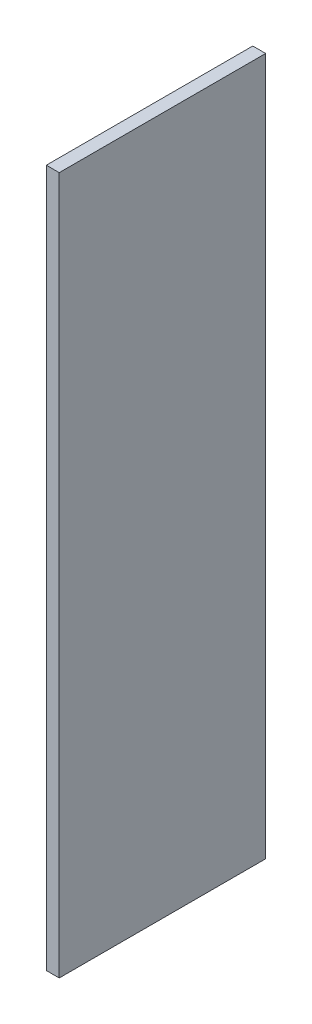
SolidWorks part; units mm, degrees
ref_plane "Front Plane" through (0, 0, 0) normal (0, 0, 1) x (1, 0, 0)
ref_plane "Top Plane" through (0, 0, 0) normal (0, 1, 0) x (1, 0, 0)
ref_plane "Right Plane" through (0, 0, 0) normal (1, 0, 0) x (0, 0, -1)
sketch "Sketch1" plane through (0, 0, 0) normal (1, 0, 0) x (0, 0, -1)
  line L1 (20.3921, -915.2196) -> (-267.6079, -915.2196)
  line L2 (20.3921, -915.2196) -> (20.3921, 57.7804)
  line L3 (20.3921, 57.7804) -> (-267.6079, 57.7804)
  line L4 (-267.6079, -915.2196) -> (-267.6079, 57.7804)
  line L5 (20.3921, -915.2196) -> (-267.6079, 57.7804) construction
  line L6 (20.3921, 57.7804) -> (-267.6079, -915.2196) construction
  point P0 (-123.6079, -428.7196)
  dimension "D1" = 288
  dimension "D2" = 973
extrude "Boss-Extrude1" add sketch "Sketch1" along normal blind 18
equation "\"H_POLKI\"=973"
equation "\"D2@Sketch1\"=\"H_POLKI\""
equation "\"DSP_WIDTH\"=18"
equation "\"D1@Boss-Extrude1\"=\"DSP_WIDTH\""
